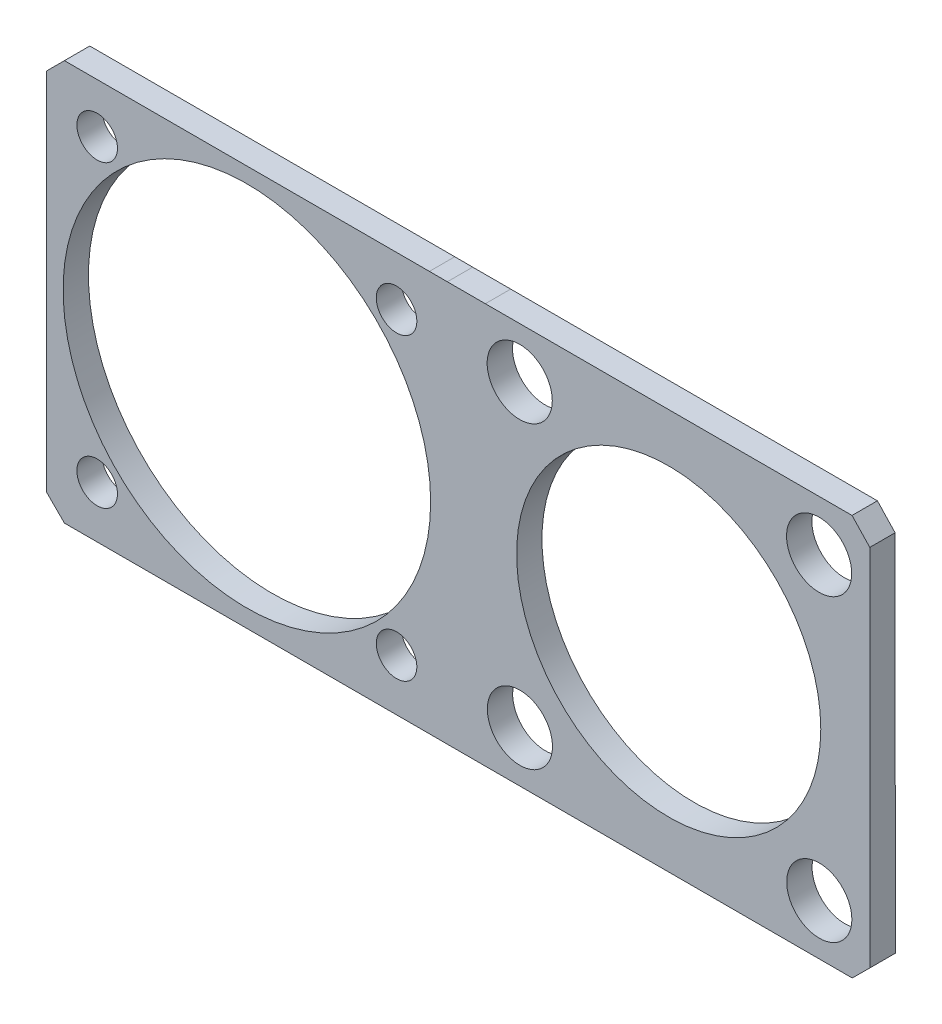
SolidWorks part; units mm, degrees
ref_plane "Front Plane" through (0, 0, 0) normal (0, 0, 1) x (1, 0, 0)
ref_plane "Top Plane" through (0, 0, 0) normal (0, 1, 0) x (1, 0, 0)
ref_plane "Right Plane" through (0, 0, 0) normal (1, 0, 0) x (0, 0, -1)
sketch "Model" plane through (0, 0, 0) normal (0, 0, 1) x (1, 0, 0)
  line L0 (6.25, 3.7) -> (3.65, 3.7)
  line L1 (6.25, -3.7) -> (6.25, 3.7)
  line L2 (6.25, -3.7) -> (3.65, -3.7)
  line L3 (3.65, 3.7) -> (3.65, -3.7)
  line L4 (22.1079, -0.1736) -> (62.4283, -0.1736) construction
  line L5 (20.0858, 19.9505) -> (18.2929, 19.9555)
  line L6 (18.2929, 19.9555) -> (-18.2831, 19.9555)
  line L7 (-18.2831, 19.9555) -> (-20.0611, 18.1775)
  line L8 (-20.0611, 18.1775) -> (-20.0611, -18.3985)
  line L9 (-20.0611, -18.3985) -> (-18.2831, -20.1765)
  line L10 (-18.2831, -20.1765) -> (18.2929, -20.1765)
  line L11 (18.2929, -20.1765) -> (20.066, -20.1814)
  line L12 (-3.65, 3.7) -> (-6.25, 3.7)
  line L13 (-3.65, 3.7) -> (-3.65, -3.7)
  line L14 (-3.65, -3.7) -> (-6.25, -3.7)
  line L15 (-6.25, -3.7) -> (-6.25, 3.7)
  line L20 (62.4382, -18.4137) -> (62.4185, 18.0665)
  line L21 (62.4185, 18.0665) -> (60.6405, 19.9506)
  line L22 (60.6405, 19.9506) -> (23.8958, 19.9506)
  line L23 (23.8958, 19.9506) -> (20.0858, 19.9505)
  line L25 (20.066, -20.1814) -> (23.876, -20.1814)
  line L26 (23.876, -20.1814) -> (60.6602, -20.1814)
  line L27 (60.6602, -20.1814) -> (62.4382, -18.4137)
  line L32 (42.2681, 19.9506) -> (42.2681, -20.1814) construction
  circle A0 centre (-15, 15) radius 2.032
  circle A1 centre (15, 15) radius 2.032
  circle A2 centre (-15, -15) radius 2.032
  circle A3 centre (15, -15) radius 2.032
  circle A4 centre (27.3402, 14.8845) radius 3.2639
  circle A5 centre (57.3402, 14.8845) radius 3.2639
  circle A6 centre (27.3583, -15.1154) radius 3.2639
  circle A7 centre (57.3582, -15.1154) radius 3.2639
  circle A8 centre (42.2681, -0.1736) radius 15.24
  circle A9 centre (0, 0) radius 18.415
  dimension "D1" = 36.576
  dimension "D19" = 4.064
  dimension "D20" = 4.064
  dimension "D21" = 4.064
  dimension "D22" = 4.064
  dimension "D24" = 30.48
  dimension "D23" = 36.83
  dimension "D2" = 36.576
  dimension "D3" = 36.576
  dimension "D4" = 3.81
  dimension "D5" = 3.81
  dimension "D6" = 1.778
  dimension "D7" = 1.778
  dimension "D8" = 1.778
  dimension "D9" = 29.9999
  dimension "D10" = 29.9999
  dimension "D11" = 29.9999
  dimension "D12" = 29.9999
  dimension "D13" = 5.066
  dimension "D14" = 4.9555
  dimension "D15" = 5.08
  dimension "D16" = 5.0611
  dimension "D17" = 29.9999
  dimension "D18" = 29.9999
extrude "Boss-Extrude1" add sketch "Model" against normal blind 2.54
